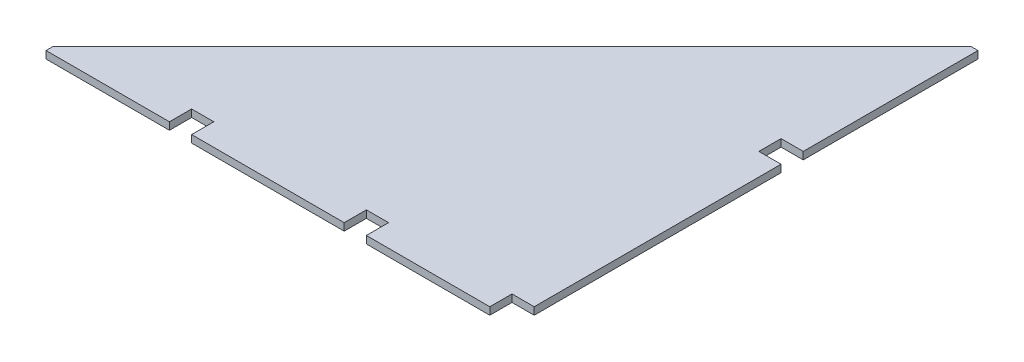
SolidWorks part; units mm, degrees
material "Pine"
ref_plane "Front Plane" through (0, 0, 0) normal (0, 0, 1) x (1, 0, 0)
ref_plane "Top Plane" through (0, 0, 0) normal (0, 1, 0) x (1, 0, 0)
ref_plane "Right Plane" through (0, 0, 0) normal (1, 0, 0) x (0, 0, -1)
sketch "Sketch1" plane through (0, 0, 0) normal (0, 1, 0) x (1, 0, 0)
  line L0 (-38.1, 0) -> (-250, 0)
  line L1 (0, 0) -> (-250, 0) construction
  line L2 (0, 0) -> (0, 461.9) construction
  line L3 (0, 800) -> (-838.1, 800) construction
  line L4 (-838.1, 0) -> (-838.1, 800) construction
  line L5 (0, 0) -> (-38.1, 0) construction
  line L6 (0, 0) -> (0, 38.1) construction
  line L7 (0, 38.1) -> (-38.1, 38.1)
  line L8 (-38.1, 0) -> (-38.1, 38.1)
  line L10 (-838.1, 0) -> (-838.1, 38.1) construction
  line L11 (-838.1, 38.1) -> (-800, 38.1) construction
  line L12 (-800, 0) -> (-800, 38.1) construction
  line L14 (-588.1, 0) -> (-588.1, 38.1)
  line L15 (-588.1, 38.1) -> (-550, 38.1)
  line L16 (-550, 0) -> (-550, 38.1)
  line L18 (-288.1, 0) -> (-288.1, 38.1)
  line L19 (-288.1, 38.1) -> (-250, 38.1)
  line L20 (-250, 0) -> (-250, 38.1)
  line L21 (-288.1, 0) -> (-550, 0) construction
  line L22 (-588.1, 0) -> (-800, 0) construction
  line L23 (-800, 0) -> (-588.1, 0)
  line L24 (-550, 0) -> (-288.1, 0)
  line L25 (0, 38.1) -> (0, 461.9)
  line L27 (-826.9, 38.1) -> (-800, 38.1) construction
  line L28 (0, 800) -> (-11.2, 800)
  line L29 (-800, 11.2) -> (-11.2, 800)
  line L30 (-800, 11.2) -> (-800, 0)
  line L31 (0, 500) -> (0, 800) construction
  line L32 (0, 461.9) -> (-38.1, 461.9)
  line L34 (0, 500) -> (-38.1, 500)
  line L35 (-38.1, 461.9) -> (-38.1, 500)
  line L36 (0, 500) -> (0, 800)
  point P8 (-11.2, 800)
  point P12 (-588.1, 0)
  point P17 (-288.1, 0)
  point P22 (-826.9, 38.1)
  point P25 (-800, 11.2)
  point P27 (0, 461.9)
  dimension "D1" = 800
  dimension "D2" = 211.9
  dimension "D3" = 38.1
  dimension "D4" = 38.1
  dimension "D5" = 11.2
  dimension "D6" = 38.1
  dimension "D7" = 38.1
  dimension "D8" = 211.9
  dimension "D9" = 38.1
  dimension "D10" = 38.1
  dimension "D11" = 261.9
  dimension "D12" = 38.1
  dimension "D13" = 38.1
  dimension "D14" = 11.2
  dimension "D15" = 11.2
  dimension "D16" = 423.8
  dimension "D17" = 38.1
  dimension "D18" = 38.1
extrude "Boss-Extrude1" add sketch "Sketch1" along normal blind 12.7
